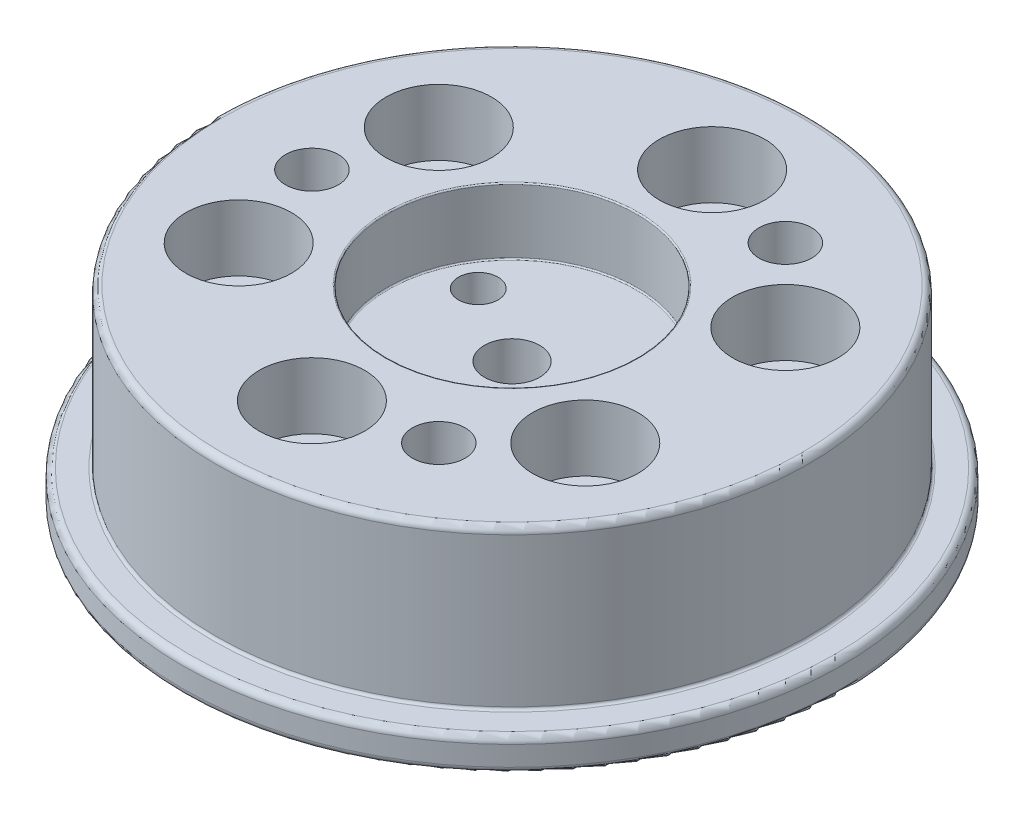
SolidWorks part; units mm, degrees
material "7075-T6, 플레이트 (SS)"
ref_plane "정면" through (0, 0, 0) normal (0, 0, 1) x (1, 0, 0)
ref_plane "윗면" through (0, 0, 0) normal (0, 1, 0) x (1, 0, 0)
ref_plane "우측면" through (0, 0, 0) normal (1, 0, 0) x (0, 0, -1)
sketch "스케치1" plane through (0, 0, 0) normal (0, 1, 0) x (1, 0, 0)
  circle A0 centre (0, 0) radius 10.1
  dimension "D1" = 20.2
extrude "보스-돌출1" add sketch "스케치1" along normal blind 2.5
sketch "스케치2" plane through (0, 2.5, 0) normal (0, 1, 0) x (1, 0, 0)
  circle A0 centre (0, 0) radius 25
  dimension "D1" = 50
extrude "보스-돌출2" add sketch "스케치2" along normal blind 2.5
sketch "스케치3" plane through (0, 5, 0) normal (0, 1, 0) x (1, 0, 0)
  circle A0 centre (0, 0) radius 22.5
  dimension "D1" = 45
extrude "보스-돌출4" add sketch "스케치3" along normal blind 12 contours A0
sketch "스케치5" plane through (0, 17, 0) normal (0, 1, 0) x (1, 0, 0)
  circle A0 centre (0, 0) radius 10
  circle A1 centre (0, 0) radius 22.5 construction
  dimension "D1" = 20
extrude "보스-돌출5" [suppressed] add sketch "스케치5" along normal blind 2
sketch "스케치6" plane through (0, 17, 0) normal (0, 1, 0) x (1, 0, 0)
  circle A0 centre (0, 0) radius 15.18 construction
  point P3 (0, 15.18)
  dimension "D1" = 30.36
hole_wizard "M4 육각 소켓 머리 캡 나사용 카운터보어1" positions "스케치7" profile "스케치8" counterbore size "M4" standard "ISO" end condition through all
sketch "스케치7" plane through (0, 17, 0) normal (0, 1, 0) x (1, 0, 0)
  point P0 (0, 15.18)
sketch "스케치8" plane through (0, 17, -15.18) normal (1, 0, 0) x (0, 0, 1)
  line L0 (0, 0) -> (0, 17)
  line L1 (0, 17) -> (2.25, 17)
  line L3 (2.25, 17) -> (2.25, 5)
  line L4 (2.25, 5) -> (4, 5)
  line L5 (4, 5) -> (4, 0)
  line L7 (4, 0) -> (0, 0)
  line L11 (0, -6.35) -> (0, 107.95) construction
  dimension "관통 구멍 지름" = 4.5
  dimension "관통 구멍 깊이" = 17
  dimension "카운터보어 지름" = 8
  dimension "카운터보어 깊이" = 5
pattern_circular "원형 패턴1" count 6 over 360 about axis through (0, 0, 0) along (0, 1, 0) of "M4 육각 소켓 머리 캡 나사용 카운터보어1"
sketch "스케치11" [suppressed] plane through (0, 19, 0) normal (0, 1, 0) x (1, 0, 0)
  circle A0 centre (0, 0) radius 5 construction
  point P3 (0, 5)
  dimension "D1" = 10
hole_wizard "M4 탭을 위한 탭 드릴1" [suppressed] positions "스케치12" profile "스케치13" hole size "M4" standard "ISO"
sketch "스케치12" [suppressed] plane through (0, 19, 0) normal (0, 1, 0) x (1, 0, 0)
  point P0 (0, 5)
sketch "스케치13" plane through (0, 19, -5) normal (1, 0, 0) x (0, 0, 1)
  line L0 (0, 0) -> (0, 5.9914)
  line L1 (0, 5.9914) -> (1.65, 5)
  line L2 (1.65, 5) -> (1.65, 0)
  line L5 (1.65, 0) -> (0, 0)
  line L10 (0, 5.9914) -> (-1.65, 5) construction
  line L11 (0, -6.35) -> (0, 107.95) construction
  dimension "구멍 지름" = 3.3
  dimension "구멍 깊이" = 5
  dimension "드릴 각도" = 118
pattern_circular "원형 패턴2" [suppressed] count 3 over 360
fillet "필렛1" radius 0.5 4 edges at (0, 0, 10.1) (0, 2.5, 25) (0, 5, 25) (0, 17, 22.5)
fillet "필렛2" radius 0.2 1 edges at (0, 5, 22.5)
fillet "필렛3" [suppressed] radius 0.1
fillet "필렛4" [suppressed] radius 0.5
sketch "스케치14" plane through (0, 17, 0) normal (0, 1, 0) x (1, 0, 0)
  circle A3 centre (0, 0) radius 15.18 construction
  point P3 (-15.18, 0)
hole_wizard "Ø4.0mm 맞춤핀 구멍1" positions "스케치15" profile "스케치17" hole size "Ø4.0" standard "ISO" end condition through all
sketch "스케치15" plane through (0, 17, 0) normal (0, 1, 0) x (1, 0, 0)
  point P0 (-15.18, 0)
sketch "스케치17" plane through (-15.18, 17, 0) normal (1, 0, 0) x (0, 0, 1)
  line L0 (0, 0) -> (0, 17)
  line L1 (0, 17) -> (2, 17)
  line L2 (2, 17) -> (2, 0)
  line L5 (2, 0) -> (0, 0)
  line L11 (0, -6.35) -> (0, 107.95) construction
  dimension "관통 구멍 지름" = 4
  dimension "관통 구멍 깊이" = 17
pattern_circular "원형 패턴3" count 3 over 360 about axis through (0, 0, 0) along (0, 1, 0) of "Ø4.0mm 맞춤핀 구멍1"
sketch "스케치18" plane through (0, 17, 0) normal (0, 1, 0) x (1, 0, 0)
  circle A0 centre (0, 0) radius 9.5
  dimension "D1" = 19
extrude "컷-돌출1" cut sketch "스케치18" against normal blind 5
sketch "스케치19" plane through (0, 12, 0) normal (0, 1, 0) x (1, 0, 0)
  circle A0 centre (0, 0) radius 5 construction
  dimension "D1" = 10
hole_wizard "M4 탭을 위한 탭 드릴2" [suppressed] positions "스케치22" profile "스케치23" hole size "M4" standard "ISO"
sketch "스케치22" plane through (0, 12, 0) normal (0, 1, 0) x (1, 0, 0)
  circle A0 centre (0, 0) radius 5 construction
  point P0 (0, 5)
sketch "스케치23" plane through (0, 12, -5) normal (1, 0, 0) x (0, 0, 1)
  line L0 (0, 0) -> (0, 5.9914)
  line L1 (0, 5.9914) -> (1.65, 5)
  line L2 (1.65, 5) -> (1.65, 0)
  line L5 (1.65, 0) -> (0, 0)
  line L10 (0, 5.9914) -> (-1.65, 5) construction
  line L11 (0, -6.35) -> (0, 107.95) construction
  dimension "구멍 지름" = 3.3
  dimension "구멍 깊이" = 5
  dimension "드릴 각도" = 118
pattern_circular "원형 패턴4" [suppressed] count 3 over 360
fillet "필렛5" radius 0.1 2 edges at (0, 12, 9.5) (0, 17, 9.5)
sketch "스케치24" plane through (0, 12, 0) normal (0, 1, 0) x (1, 0, 0)
  circle A0 centre (0, 0) radius 7 construction
  dimension "D1" = 14
hole_wizard "Ø3.0mm 맞춤핀 구멍1" positions "스케치25" profile "스케치26" hole size "Ø3.0" standard "ISO"
sketch "스케치25" plane through (0, 12, 0) normal (0, 1, 0) x (1, 0, 0)
  circle A0 centre (0, 0) radius 7 construction
  point P0 (0, -7)
sketch "스케치26" plane through (0, 12, 7) normal (1, 0, 0) x (0, 0, 1)
  line L0 (0, 0) -> (0, 5.9013)
  line L1 (0, 5.9013) -> (1.5, 5)
  line L2 (1.5, 5) -> (1.5, 0)
  line L5 (1.5, 0) -> (0, 0)
  line L10 (0, 5.9013) -> (-1.5, 5) construction
  line L11 (0, -6.35) -> (0, 107.95) construction
  dimension "구멍 지름" = 3
  dimension "구멍 깊이" = 5
  dimension "드릴 각도" = 118
pattern_circular "원형 패턴5" count 3 over 360 about axis through (0, 0, 0) along (0, 1, 0) of "Ø3.0mm 맞춤핀 구멍1"
hole_wizard "M5 탭을 위한 탭 드릴1" positions "스케치27" profile "스케치28" hole size "M5" standard "ISO" end condition through all
sketch "스케치27" plane through (0, 12, 0) normal (0, 1, 0) x (1, 0, 0)
  point P0 (0, 0)
sketch "스케치28" plane through (0, 12, 0) normal (1, 0, 0) x (0, 0, 1)
  line L0 (0, 0) -> (0, 12)
  line L1 (0, 12) -> (2.1, 12)
  line L2 (2.1, 12) -> (2.1, 0)
  line L5 (2.1, 0) -> (0, 0)
  line L11 (0, -6.35) -> (0, 107.95) construction
  dimension "관통 구멍 지름" = 4.2
  dimension "관통 구멍 깊이" = 12
